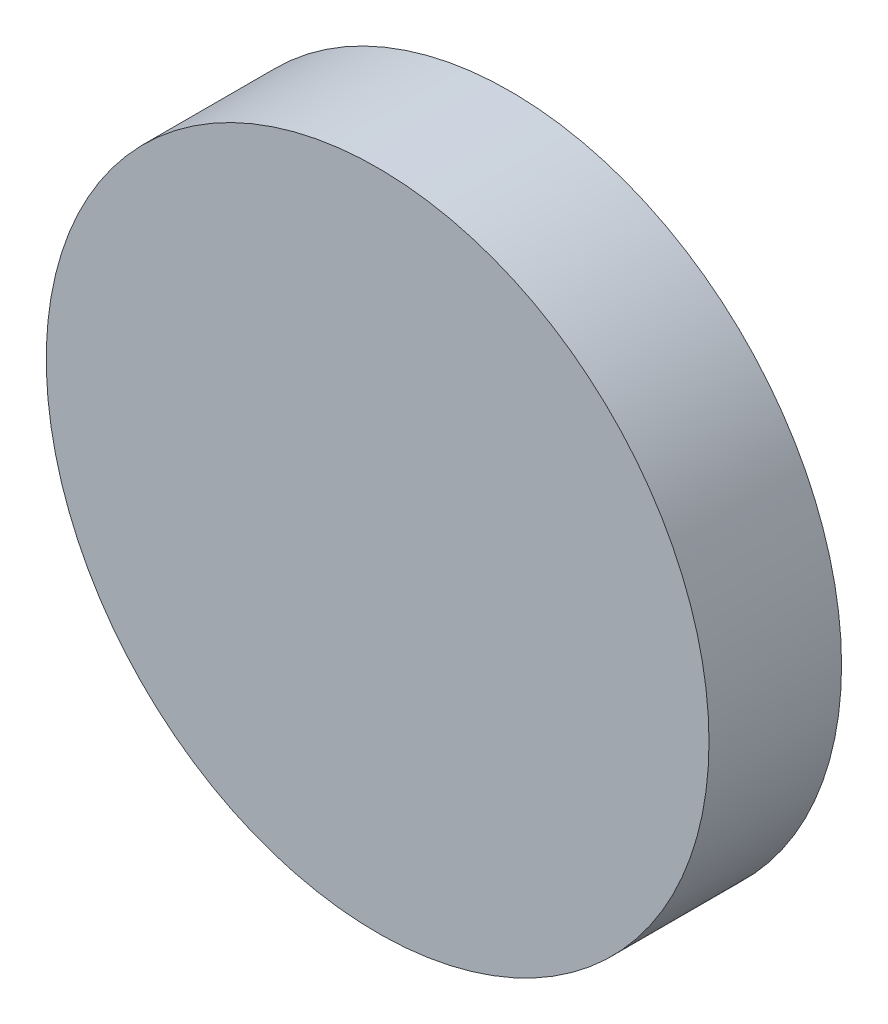
SolidWorks part; units mm, degrees
ref_plane "前视基准面" through (0, 0, 0) normal (0, 0, 1) x (1, 0, 0)
ref_plane "上视基准面" through (0, 0, 0) normal (0, 1, 0) x (1, 0, 0)
ref_plane "右视基准面" through (0, 0, 0) normal (1, 0, 0) x (0, 0, -1)
sketch "草图1" plane through (0, 0, 0) normal (0, 0, 1) x (1, 0, 0)
  circle A0 centre (0, 0) radius 15
  dimension "D1" = 30
extrude "凸台-拉伸1" add sketch "草图1" along normal blind 6
